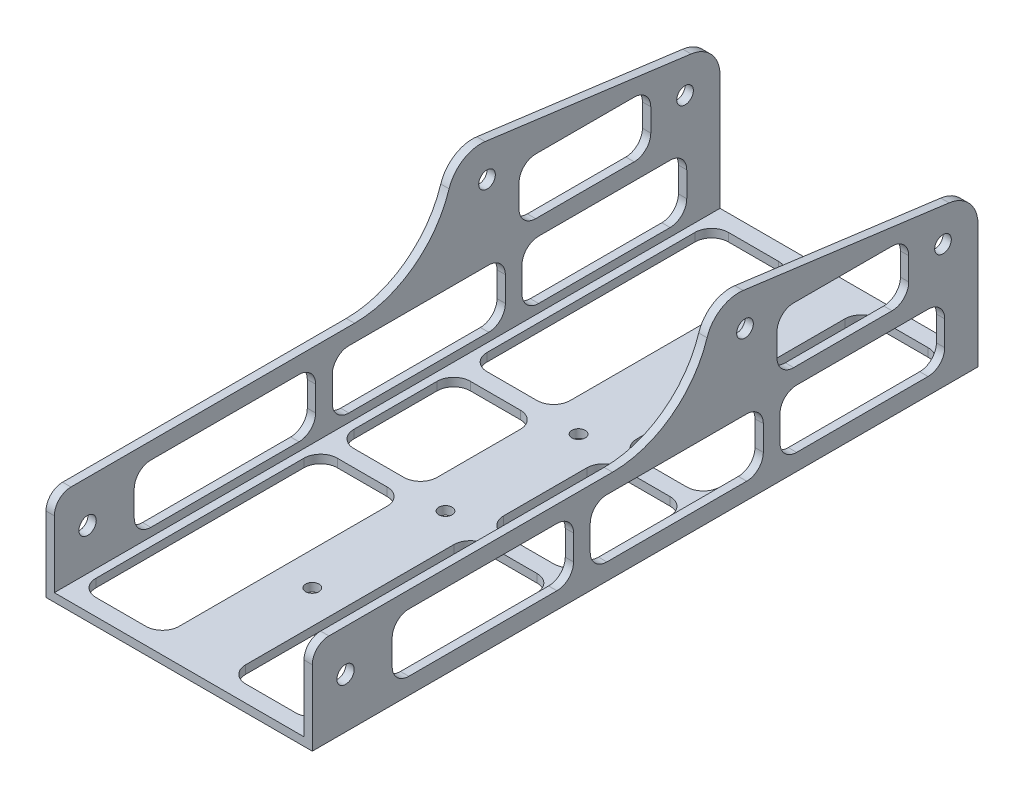
SolidWorks part; units mm, degrees
ref_plane "Front Plane" through (0, 0, 0) normal (0, 0, 1) x (1, 0, 0)
ref_plane "Top Plane" through (0, 0, 0) normal (0, 1, 0) x (1, 0, 0)
ref_plane "Right Plane" through (0, 0, 0) normal (1, 0, 0) x (0, 0, -1)
sketch "Sketch1" plane through (0, 0, 0) normal (0, 0, 1) x (1, 0, 0)
  line L0 (0, 0) -> (0, 73.025)
  line L1 (0, 73.025) -> (3.175, 73.025)
  line L2 (3.175, 73.025) -> (3.175, 3.175)
  line L3 (3.175, 3.175) -> (98.425, 3.175)
  line L4 (98.425, 3.175) -> (98.425, 73.025)
  line L5 (98.425, 73.025) -> (101.6, 73.025)
  line L6 (101.6, 73.025) -> (101.6, 0)
  line L7 (101.6, 0) -> (0, 0)
  dimension "D1" = 3.175
  dimension "D2" = 3.175
  dimension "D3" = 3.175
  dimension "D4" = 101.6
  dimension "D5" = 69.85
  dimension "D6" = 69.85
extrude "Boss-Extrude1" add sketch "Sketch1" along normal blind 254
sketch "Sketch2" plane through (101.6, 0, 0) normal (1, 0, 0) x (0, 0, -1)
  line L0 (-254, 0) -> (-254, 73.025) construction
  line L1 (-254, 0) -> (0, 0) construction
  circle A0 centre (-241.3, 19.05) radius 3.302
  circle A1 centre (-88.9, 57.15) radius 3.175
  dimension "D1" = 6.604
  dimension "D4" = 6.35
  dimension "D2" = 152.4
  dimension "D3" = 12.7
  dimension "D5" = 19.05
  dimension "D6" = 57.15
extrude "Cut-Extrude1" cut sketch "Sketch2" against normal blind 203.2
sketch "Sketch3" plane through (0, 3.175, 0) normal (0, 1, 0) x (1, 0, 0)
  line L2 (98.425, 0) -> (3.175, 0) construction
  line L4 (50.8, 0) -> (50.8, -254) construction
  line L5 (98.425, -254) -> (3.175, -254) construction
  circle A0 centre (50.8, -50.8) radius 2.54
  circle A1 centre (50.8, -101.6) radius 2.54
  circle A2 centre (50.8, -152.4) radius 2.54
  circle A3 centre (50.8, -203.2) radius 2.54
  dimension "D1" = 5.08
  dimension "D2" = 50.8
  dimension "D5" = 50.8
  dimension "D3" = 50.8
  dimension "D4" = 50.8
extrude "Cut-Extrude2" cut sketch "Sketch3" against normal blind 9.525
sketch "Sketch4" plane through (101.6, 0, 0) normal (1, 0, 0) x (0, 0, -1)
  line L1 (-254, 73.025) -> (-101.6, 73.025)
  line L2 (-254, 73.025) -> (-254, 34.925)
  line L3 (-254, 34.925) -> (-139.446, 34.925)
  line L4 (-101.6, 73.025) -> (-101.6, 72.771)
  arc A0 (-139.446, 34.925) -> (-101.6, 72.771) centre (-139.446, 72.771) ccw
  dimension "D3" = 37.846
  dimension "D1" = 38.1
  dimension "D2" = 152.4
extrude "Cut-Extrude3" cut sketch "Sketch4" against normal through all
sketch "Sketch5" plane through (0, 0, 0) normal (-1, 0, 0) x (0, 0, 1)
  line L0 (88.9, 57.15) -> (13.3519, 47.2039) construction
  line L1 (88.9, 57.15) -> (0, 57.15) construction
  line L2 (0, 73.025) -> (0, 0) construction
  circle A0 centre (88.9, 57.15) radius 3.175 construction
  circle A3 centre (88.9, 57.15) radius 3.175
  circle A4 centre (13.3519, 47.2039) radius 3.175
  dimension "D3" = 7.5
  dimension "D2" = 76.2
extrude "Cut-Extrude4" cut sketch "Sketch5" against normal through all contours A4
sketch "Sketch6" plane through (0, 0, 0) normal (-1, 0, 0) x (0, 0, 1)
  line L0 (13.3519, 47.2039) -> (88.9, 57.15) construction
  line L1 (11.6942, 59.7953) -> (117.2593, 73.6932)
  line L2 (11.6942, 59.7953) -> (-12.4817, 56.6124)
  line L3 (-12.4817, 56.6124) -> (-7.0221, 78.936)
  line L4 (-7.0221, 78.936) -> (117.2593, 83.6489)
  line L5 (117.2593, 83.6489) -> (117.2593, 62.8772)
  line L6 (11.6942, 59.7953) -> (87.2423, 69.7413) construction
  arc M4 (139.446, 34.925) -> (101.6, 72.771) centre (139.446, 72.771) cw
  line M5 (101.6, 72.771) -> (101.6, 73.025)
  line M6 (101.6, 73.025) -> (0, 73.025)
  line M7 (0, 73.025) -> (0, 0)
  dimension "D1" = 12.7
extrude "Cut-Extrude6" cut sketch "Sketch6" against normal through all contours L5 L4 L3 L2 L1 M7 M6 M5 M4 | L2 L1 M4 M5 M6 M7
fillet "Fillet1" radius 12.7 4 edges at (100.0125, 58.2557, 0) (1.5875, 58.2557, 0) (100.0125, 71.6338, 101.6171) (1.5875, 71.6338, 101.6171)
fillet "Fillet2" radius 6.35 2 edges at (100.0125, 34.925, 254) (1.5875, 34.925, 254)
sketch "Sketch7" plane through (0, 0, 0) normal (-1, 0, 0) x (0, 0, 1)
  line L0 (19.05, 6.35) -> (69.215, 6.35)
  line L1 (12.7, 12.7) -> (12.7, 22.225)
  line L2 (217.17, 28.575) -> (160.655, 28.575)
  line L3 (223.52, 22.225) -> (223.52, 12.7)
  line L4 (70.3422, 56.2887) -> (32.7762, 56.2887)
  line L5 (254, 0) -> (254, 28.575)
  line L6 (247.65, 34.925) -> (139.446, 34.925)
  line L7 (89.6162, 70.0539) -> (11.0423, 59.7094)
  line L8 (0, 47.1181) -> (0, 0)
  line L9 (0, 0) -> (254, 0)
  line L10 (254, 0) -> (254, 28.575)
  line L11 (247.65, 34.925) -> (139.446, 34.925)
  line L12 (89.6162, 70.0539) -> (11.0423, 59.7094)
  line L13 (0, 47.1181) -> (0, 0)
  line L14 (0, 0) -> (254, 0)
  line L15 (70.3422, 34.925) -> (32.7762, 34.925)
  line L16 (26.4262, 49.9387) -> (26.4262, 41.275)
  line L17 (76.6922, 49.9387) -> (76.6922, 41.275)
  line L18 (88.265, 6.35) -> (141.605, 6.35)
  line L20 (160.655, 6.35) -> (217.17, 6.35)
  line L21 (223.52, 34.925) -> (6.35, 34.925) construction
  line L22 (75.565, 22.225) -> (75.565, 12.7)
  line L23 (147.955, 22.225) -> (147.955, 12.7)
  line L24 (81.915, 22.225) -> (81.915, 12.7)
  line L25 (154.305, 22.225) -> (154.305, 12.7)
  line L26 (69.215, 28.575) -> (19.05, 28.575)
  line L27 (141.605, 28.575) -> (88.265, 28.575)
  line L28 (223.52, 28.575) -> (6.35, 28.575) construction
  circle A0 centre (13.3519, 47.2039) radius 3.175 construction
  circle A1 centre (13.3519, 47.2039) radius 3.175
  circle A2 centre (88.9, 57.15) radius 3.175 construction
  circle A3 centre (88.9, 57.15) radius 3.175
  arc A4 (254, 28.575) -> (247.65, 34.925) centre (247.65, 28.575) ccw
  arc A5 (103.3775, 61.3089) -> (139.446, 34.925) centre (139.446, 72.771) ccw
  arc A6 (103.3775, 61.3089) -> (89.6162, 70.0539) centre (91.2739, 57.4625) ccw
  arc A7 (11.0423, 59.7094) -> (0, 47.1181) centre (12.7, 47.1181) ccw
  arc A8 (254, 28.575) -> (247.65, 34.925) centre (247.65, 28.575) ccw
  arc A9 (103.3775, 61.3089) -> (139.446, 34.925) centre (139.446, 72.771) ccw
  arc A10 (103.3775, 61.3089) -> (89.6162, 70.0539) centre (91.2739, 57.4625) ccw
  arc A11 (11.0423, 59.7094) -> (0, 47.1181) centre (12.7, 47.1181) ccw
  circle A12 centre (13.3519, 47.2039) radius 12.7
  circle A13 centre (88.9, 57.15) radius 12.7
  circle A14 centre (241.3, 19.05) radius 12.7
  arc A15 (70.3422, 34.925) -> (76.6922, 41.275) centre (70.3422, 41.275) ccw
  arc A16 (76.6922, 49.9387) -> (70.3422, 56.2887) centre (70.3422, 49.9387) ccw
  arc A17 (26.4262, 49.9387) -> (32.7762, 56.2887) centre (32.7762, 49.9387) cw
  arc A18 (26.4262, 41.275) -> (32.7762, 34.925) centre (32.7762, 41.275) ccw
  arc A19 (217.17, 6.35) -> (223.52, 12.7) centre (217.17, 12.7) ccw
  arc A20 (217.17, 28.575) -> (223.52, 22.225) centre (217.17, 22.225) cw
  arc A21 (154.305, 22.225) -> (160.655, 28.575) centre (160.655, 22.225) cw
  arc A22 (154.305, 12.7) -> (160.655, 6.35) centre (160.655, 12.7) ccw
  arc A23 (147.955, 12.7) -> (141.605, 6.35) centre (141.605, 12.7) cw
  arc A24 (147.955, 22.225) -> (141.605, 28.575) centre (141.605, 22.225) ccw
  arc A25 (81.915, 22.225) -> (88.265, 28.575) centre (88.265, 22.225) cw
  arc A26 (81.915, 12.7) -> (88.265, 6.35) centre (88.265, 12.7) ccw
  arc A27 (19.05, 6.35) -> (12.7, 12.7) centre (19.05, 12.7) cw
  arc A28 (69.215, 6.35) -> (75.565, 12.7) centre (69.215, 12.7) ccw
  arc A29 (75.565, 22.225) -> (69.215, 28.575) centre (69.215, 22.225) ccw
  arc A30 (19.05, 28.575) -> (12.7, 22.225) centre (19.05, 22.225) ccw
  point P24 (91.1239, 58.6021)
  point P29 (12.55, 48.2577)
  point P47 (223.52, 6.35)
  point P49 (0, 0)
  point P73 (12.7, 6.35)
  point P81 (69.215, 48.2047)
  point P82 (34.6364, 51.1654)
  point P83 (32.7762, 58.3242)
  dimension "D2" = 6.35
  dimension "D3" = 6.35
  dimension "D7" = 6.35
  dimension "D8" = 6.35
  dimension "D9" = 6.35
  dimension "D4" = 12.7
  dimension "8" = 210.82
  dimension "D1" = 0
  dimension "D6" = 6.35
extrude "Cut-Extrude7" cut sketch "Sketch7" against normal through all contours L16 A18 L15 A15 L17 A16 L4 A17 | L26 A30 L1 A27 L0 A28 L22 A29 | L24 A26 L18 A23 L23 A24 L27 A25 | L25 A22 L20 A19 L3 A20 L2 A21
sketch "Sketch8" plane through (0, 0, 0) normal (0, -1, 0) x (1, 0, 0)
  line L0 (12.7, 6.35) -> (31.75, 6.35)
  line L1 (95.25, 6.35) -> (95.25, 247.65)
  line L2 (95.25, 247.65) -> (50.8, 247.65)
  line L3 (6.35, 241.3) -> (6.35, 212.725)
  line L4 (0, 0) -> (101.6, 0)
  line L5 (101.6, 0) -> (101.6, 254)
  line L6 (101.6, 254) -> (0, 254)
  line L7 (0, 254) -> (0, 0)
  line L8 (0, 0) -> (101.6, 0)
  line L9 (101.6, 0) -> (101.6, 254)
  line L10 (101.6, 254) -> (0, 254)
  line L11 (0, 254) -> (0, 0)
  line L12 (38.1, 241.3) -> (38.1, 212.725)
  line L13 (50.8, 247.65) -> (50.8, 6.35) construction
  line L14 (50.8, 203.2) -> (38.1, 203.2)
  line L15 (50.8, 152.4) -> (38.1, 152.4)
  line L16 (50.8, 101.6) -> (38.1, 101.6)
  line L17 (50.8, 50.8) -> (38.1, 50.8)
  line L18 (31.75, 206.375) -> (12.7, 206.375)
  line L19 (50.8, 155.575) -> (38.5033, 155.575)
  line L20 (50.8, 104.775) -> (38.5033, 104.775)
  line L21 (50.8, 53.975) -> (38.5033, 53.975)
  line L22 (50.8, 200.025) -> (38.5033, 200.025)
  line L23 (50.8, 149.225) -> (38.5033, 149.225)
  line L24 (50.8, 98.425) -> (38.5033, 98.425)
  line L25 (50.8, 47.625) -> (38.5033, 47.625)
  line L26 (38.1, 193.675) -> (38.1, 161.925)
  line L27 (6.35, 193.675) -> (6.35, 161.925)
  line L28 (50.8, 203.2) -> (6.35, 203.2) construction
  line L29 (31.75, 200.025) -> (12.7, 200.025)
  line L30 (6.35, 247.65) -> (6.35, 6.35) construction
  line L31 (50.8, 206.375) -> (6.35, 206.375) construction
  line L32 (31.75, 247.65) -> (12.7, 247.65)
  line L33 (50.8, 200.025) -> (6.35, 200.025) construction
  line L34 (31.75, 155.575) -> (12.7, 155.575)
  line L35 (95.25, 247.65) -> (6.35, 247.65) construction
  line L36 (38.1, 142.875) -> (38.1, 111.125)
  line L37 (50.8, 155.575) -> (6.35, 155.575) construction
  line L38 (6.35, 142.875) -> (6.35, 111.125)
  line L39 (31.75, 149.225) -> (12.7, 149.225)
  line L40 (50.8, 152.4) -> (6.35, 152.4) construction
  line L41 (31.75, 104.775) -> (12.7, 104.775)
  line L42 (50.8, 149.225) -> (6.35, 149.225) construction
  line L43 (38.1, 92.075) -> (38.1, 60.325)
  line L44 (50.8, 104.775) -> (6.35, 104.775) construction
  line L45 (6.35, 92.075) -> (6.35, 60.325)
  line L46 (31.75, 98.425) -> (12.7, 98.425)
  line L47 (50.8, 101.6) -> (6.35, 101.6) construction
  line L48 (6.35, 41.275) -> (6.35, 12.7)
  line L49 (50.8, 98.425) -> (6.35, 98.425) construction
  line L50 (38.1, 41.275) -> (38.1, 12.7)
  line L51 (50.8, 50.8) -> (6.35, 50.8) construction
  line L52 (31.75, 53.975) -> (12.7, 53.975)
  line L53 (31.75, 47.625) -> (12.7, 47.625)
  line L54 (50.8, 53.975) -> (6.35, 53.975) construction
  line L55 (50.8, 6.35) -> (95.25, 6.35)
  line L56 (50.8, 47.625) -> (6.35, 47.625) construction
  line L57 (95.25, 41.275) -> (95.25, 12.7)
  line L58 (6.35, 6.35) -> (95.25, 6.35) construction
  line L59 (69.85, 47.625) -> (88.9, 47.625)
  line L60 (63.5, 41.275) -> (63.5, 12.7)
  line L61 (88.9, 6.35) -> (69.85, 6.35)
  line L62 (69.85, 98.425) -> (88.9, 98.425)
  line L63 (63.5, 92.075) -> (63.5, 60.325)
  line L64 (69.85, 53.975) -> (88.9, 53.975)
  line L65 (95.25, 92.075) -> (95.25, 60.325)
  line L66 (69.85, 149.225) -> (88.9, 149.225)
  line L67 (63.5, 142.875) -> (63.5, 111.125)
  line L68 (69.85, 104.775) -> (88.9, 104.775)
  line L69 (95.25, 142.875) -> (95.25, 111.125)
  line L70 (69.85, 200.025) -> (88.9, 200.025)
  line L71 (63.5, 193.675) -> (63.5, 161.925)
  line L72 (69.85, 155.575) -> (88.9, 155.575)
  line L73 (95.25, 193.675) -> (95.25, 161.925)
  line L74 (69.85, 247.65) -> (88.9, 247.65)
  line L75 (63.5, 241.3) -> (63.5, 212.725)
  line L76 (69.85, 206.375) -> (88.9, 206.375)
  line L77 (95.25, 241.3) -> (95.25, 212.725)
  line L78 (6.35, 212.725) -> (6.35, 193.675)
  line L79 (38.1, 193.675) -> (38.1, 212.725)
  line L80 (6.35, 60.325) -> (6.35, 41.275)
  line L81 (38.1, 41.275) -> (38.1, 60.325)
  line L82 (63.5, 212.725) -> (63.5, 193.675)
  line L83 (95.25, 193.675) -> (95.25, 212.725)
  line L84 (63.5, 60.325) -> (63.5, 41.275)
  line L85 (95.25, 41.275) -> (95.25, 60.325)
  circle A0 centre (50.8, 203.2) radius 12.7
  circle A1 centre (50.8, 50.8) radius 2.54
  circle A2 centre (50.8, 50.8) radius 2.54
  circle A3 centre (50.8, 101.6) radius 2.54
  circle A4 centre (50.8, 101.6) radius 2.54
  circle A5 centre (50.8, 152.4) radius 2.54
  circle A6 centre (50.8, 152.4) radius 2.54
  circle A7 centre (50.8, 203.2) radius 2.54
  circle A8 centre (50.8, 203.2) radius 2.54
  circle A9 centre (50.8, 152.4) radius 12.7
  circle A10 centre (50.8, 101.6) radius 12.7
  circle A11 centre (50.8, 50.8) radius 12.7
  arc A12 (12.7, 6.35) -> (6.35, 12.7) centre (12.7, 12.7) cw
  arc A13 (38.1, 12.7) -> (31.75, 6.35) centre (31.75, 12.7) cw
  arc A14 (38.1, 41.275) -> (31.75, 47.625) centre (31.75, 41.275) ccw
  arc A15 (12.7, 47.625) -> (6.35, 41.275) centre (12.7, 41.275) ccw
  arc A16 (38.1, 92.075) -> (31.75, 98.425) centre (31.75, 92.075) ccw
  arc A17 (12.7, 98.425) -> (6.35, 92.075) centre (12.7, 92.075) ccw
  arc A18 (6.35, 111.125) -> (12.7, 104.775) centre (12.7, 111.125) ccw
  arc A19 (31.75, 104.775) -> (38.1, 111.125) centre (31.75, 111.125) ccw
  arc A20 (38.1, 142.875) -> (31.75, 149.225) centre (31.75, 142.875) ccw
  arc A21 (12.7, 149.225) -> (6.35, 142.875) centre (12.7, 142.875) ccw
  arc A22 (6.35, 161.925) -> (12.7, 155.575) centre (12.7, 161.925) ccw
  arc A23 (31.75, 155.575) -> (38.1, 161.925) centre (31.75, 161.925) ccw
  arc A24 (38.1, 193.675) -> (31.75, 200.025) centre (31.75, 193.675) ccw
  arc A25 (12.7, 200.025) -> (6.35, 193.675) centre (12.7, 193.675) ccw
  arc A26 (12.7, 206.375) -> (6.35, 212.725) centre (12.7, 212.725) cw
  arc A27 (38.1, 212.725) -> (31.75, 206.375) centre (31.75, 212.725) cw
  arc A28 (38.1, 241.3) -> (31.75, 247.65) centre (31.75, 241.3) ccw
  arc A29 (12.7, 247.65) -> (6.35, 241.3) centre (12.7, 241.3) ccw
  arc A30 (12.7, 53.975) -> (6.35, 60.325) centre (12.7, 60.325) cw
  arc A31 (38.1, 60.325) -> (31.75, 53.975) centre (31.75, 60.325) cw
  arc A32 (88.9, 47.625) -> (95.25, 41.275) centre (88.9, 41.275) cw
  arc A33 (63.5, 41.275) -> (69.85, 47.625) centre (69.85, 41.275) cw
  arc A34 (88.9, 6.35) -> (95.25, 12.7) centre (88.9, 12.7) ccw
  arc A35 (63.5, 12.7) -> (69.85, 6.35) centre (69.85, 12.7) ccw
  arc A36 (63.5, 92.075) -> (69.85, 98.425) centre (69.85, 92.075) cw
  arc A37 (63.5, 60.325) -> (69.85, 53.975) centre (69.85, 60.325) ccw
  arc A38 (88.9, 98.425) -> (95.25, 92.075) centre (88.9, 92.075) cw
  arc A39 (88.9, 53.975) -> (95.25, 60.325) centre (88.9, 60.325) ccw
  arc A40 (63.5, 142.875) -> (69.85, 149.225) centre (69.85, 142.875) cw
  arc A41 (69.85, 104.775) -> (63.5, 111.125) centre (69.85, 111.125) cw
  arc A42 (95.25, 111.125) -> (88.9, 104.775) centre (88.9, 111.125) cw
  arc A43 (88.9, 149.225) -> (95.25, 142.875) centre (88.9, 142.875) cw
  arc A44 (63.5, 193.675) -> (69.85, 200.025) centre (69.85, 193.675) cw
  arc A45 (69.85, 155.575) -> (63.5, 161.925) centre (69.85, 161.925) cw
  arc A46 (95.25, 161.925) -> (88.9, 155.575) centre (88.9, 161.925) cw
  arc A47 (88.9, 200.025) -> (95.25, 193.675) centre (88.9, 193.675) cw
  arc A48 (63.5, 241.3) -> (69.85, 247.65) centre (69.85, 241.3) cw
  arc A49 (63.5, 212.725) -> (69.85, 206.375) centre (69.85, 212.725) ccw
  arc A50 (88.9, 206.375) -> (95.25, 212.725) centre (88.9, 212.725) ccw
  arc A51 (88.9, 247.65) -> (95.25, 241.3) centre (88.9, 241.3) cw
  point P74 (38.1, 47.625)
  point P80 (38.1, 98.425)
  point P91 (38.1, 149.225)
  point P102 (38.1, 200.025)
  point P113 (38.1, 247.65)
  point P122 (38.1, 53.975)
  dimension "D6" = 6.35
  dimension "1" = 25.4
  dimension "D9" = 6.35
  dimension "D10" = 6.35
  dimension "D7" = 3.175
  dimension "D1" = 0
  dimension "D2" = 0
  dimension "D3" = 0
  dimension "D4" = 0
  dimension "D5" = 0
  dimension "D8" = 3.175
extrude "Cut-Extrude8" cut sketch "Sketch8" against normal blind 116.332 contours L32 A29 L3 A26 L18 A27 L12 A28 | A51 L2 A48 L75 A49 L76 A50 L1 | L29 A25 L27 A22 L34 A23 L26 A24 | A47 L70 A44 L71 A45 L72 A46 L1 | L39 A21 L38 A18 L41 A19 L36 A20 | A43 L66 A40 L67 A41 L68 A42 L1 | A31 L43 A16 L46 A17 L45 A30 L52 | L64 A39 L1 A38 L62 A36 L63 A37 | L53 A15 L48 A12 L0 A13 L50 A14 | L60 A35 L55 A34 L1 A32 L59 A33 | L79 A27 L18 A26 L78 A25 L29 A24 | L81 A31 L52 A30 L80 A15 L53 A14 | A50 L76 A49 L82 A44 L70 A47 L1 | A39 L64 A37 L84 A33 L59 A32 L1
